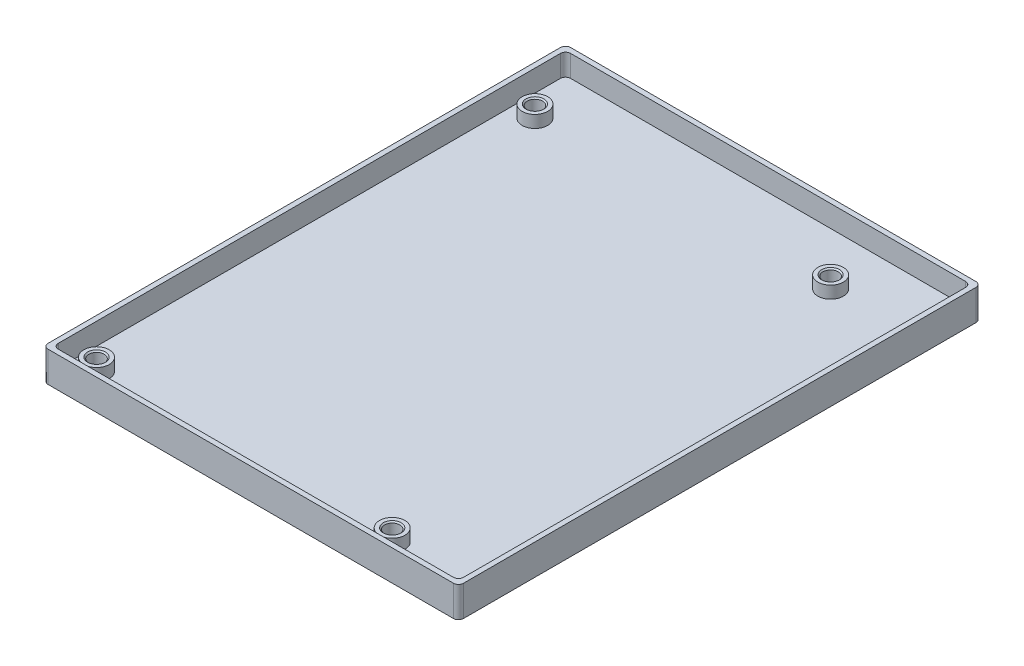
SolidWorks part; units mm, degrees
ref_plane "Front Plane" through (0, 0, 0) normal (0, 0, 1) x (1, 0, 0)
ref_plane "Top Plane" through (0, 0, 0) normal (0, 1, 0) x (1, 0, 0)
ref_plane "Right Plane" through (0, 0, 0) normal (1, 0, 0) x (0, 0, -1)
sketch "Sketch1" plane through (0, 0, 0) normal (0, 1, 0) x (1, 0, 0)
  line L1 (-40.75, -51.25) -> (40.75, -51.25)
  line L2 (-40.75, -51.25) -> (-40.75, 51.25)
  line L3 (-40.75, 51.25) -> (40.75, 51.25)
  line L4 (40.75, -51.25) -> (40.75, 51.25)
  line L5 (-40.75, -51.25) -> (40.75, 51.25) construction
  line L6 (-40.75, 51.25) -> (40.75, -51.25) construction
  point P0 (0, 0)
  dimension "D1" = 81.5
  dimension "D2" = 102.5
extrude "Boss-Extrude1" add sketch "Sketch1" along normal blind 6 contours L2 L3 L4 L1
sketch "Sketch2" plane through (0, 6, 0) normal (0, 1, 0) x (1, 0, 0)
  line L0 (39.5, -50) -> (39.5, 50) construction
  line L7 (39.5, -50) -> (-39.5, -50) construction
  line L8 (-39.5, -50) -> (-39.5, 50) construction
  line L9 (39.5, 50) -> (-39.5, 50) construction
  line L10 (39.5, -50) -> (-39.5, 50) construction
  line L11 (-39.5, -50) -> (39.5, 50) construction
  circle A8 centre (-35.5, -46) radius 1.5
  circle A9 centre (-35.5, 40) radius 1.5
  circle A10 centre (22.5, -46) radius 1.5
  circle A11 centre (22.5, 40) radius 1.5
  point P0 (0, 0)
  dimension "D2" = 4
  dimension "D6" = 3
  dimension "D1" = 79
  dimension "D3" = 4
  dimension "D4" = 10
  dimension "D5" = 17
  dimension "D7" = 100
extrude "Cut-Extrude1" cut sketch "Sketch2" against normal through all
sketch "Sketch7" plane through (0, 6, 0) normal (0, 1, 0) x (1, 0, 0)
  line L0 (-40.75, -51.25) -> (-40.75, 51.25) construction
  line L1 (39.75, -50.25) -> (-39.75, -50.25)
  line L2 (39.75, -50.25) -> (39.75, 50.25)
  line L3 (39.75, 50.25) -> (-39.75, 50.25)
  line L4 (-39.75, -50.25) -> (-39.75, 50.25)
  line L5 (39.75, -50.25) -> (-39.75, 50.25) construction
  line L6 (39.75, 50.25) -> (-39.75, -50.25) construction
  line L7 (-40.75, 51.25) -> (40.75, 51.25) construction
  point P0 (0, 0)
  dimension "D1" = 1
  dimension "D2" = 1
extrude "Cut-Extrude3" cut sketch "Sketch7" against normal blind 1.85
sketch "Sketch8" plane through (0, 4.15, 0) normal (0, 1, 0) x (1, 0, 0)
  line L19 (-39.75, 50.25) -> (39.75, 50.25)
  line L20 (-39.75, 50.25) -> (-39.75, -50.25)
  line L21 (-39.75, -50.25) -> (39.75, -50.25)
  line L22 (39.75, 50.25) -> (39.75, -50.25)
  circle A0 centre (-35.5, 40) radius 2.5
  circle A1 centre (22.5, 40) radius 2.5
  circle A2 centre (-35.5, -46) radius 2.5
  circle A3 centre (22.5, -46) radius 2.5
  dimension "D1" = 5
extrude "Cut-Extrude4" cut sketch "Sketch8" against normal blind 2.4
fillet "Fillet1" radius 1 8 edges at (-40.75, 3, 51.25) (40.75, 3, 51.25) (40.75, 3, -51.25) (-40.75, 3, -51.25) (39.75, 3.875, -50.25) (39.75, 3.875, 50.25) (-39.75, 3.875, 50.25) (-39.75, 3.875, -50.25)
chamfer "Chamfer1" distance 0.25 angle 45 4 edges at (-35.5, 4.15, 47.5) (22.5, 4.15, 47.5) (22.5, 4.15, -38.5) (-35.5, 4.15, -38.5)
